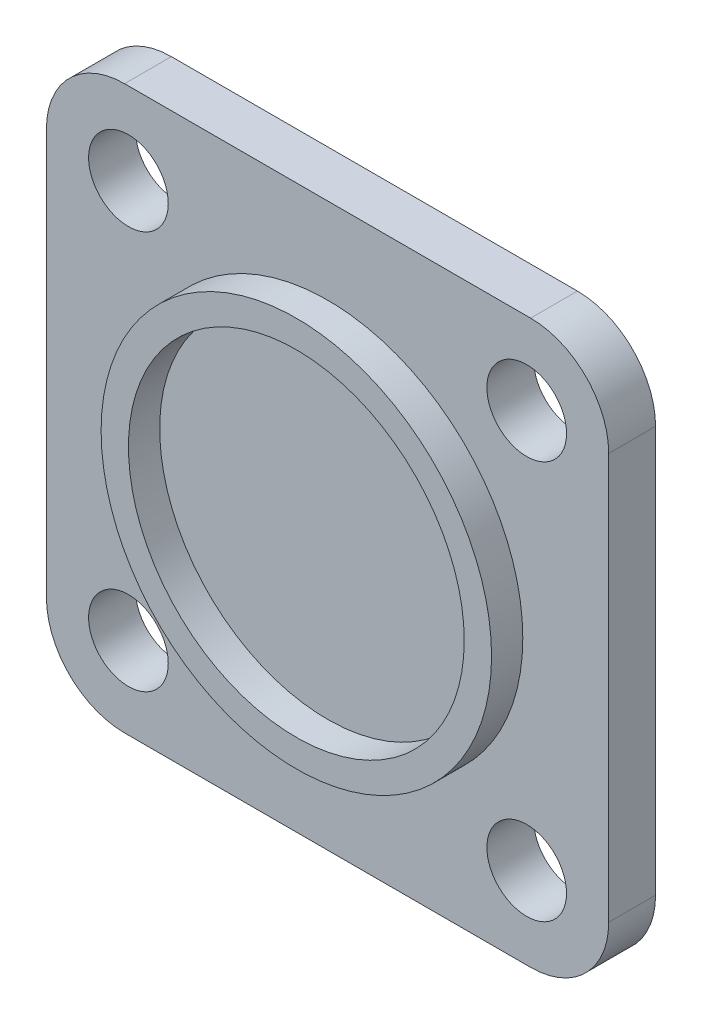
SolidWorks part; units mm, degrees
ref_plane "Płaszczyzna przednia" through (0, 0, 0) normal (0, 0, 1) x (1, 0, 0)
ref_plane "Płaszczyzna górna" through (0, 0, 0) normal (0, 1, 0) x (1, 0, 0)
ref_plane "Płaszczyzna prawa" through (0, 0, 0) normal (1, 0, 0) x (0, 0, -1)
sketch "Szkic1" plane through (0, 0, 0) normal (0, 0, 1) x (1, 0, 0)
  line L1 (-3.0269, 2.1836) -> (22.9731, 2.1836)
  line L2 (-8.0269, -2.8164) -> (-8.0269, -28.8164)
  line L3 (-3.0269, -33.8164) -> (22.9731, -33.8164)
  line L4 (27.9731, -2.8164) -> (27.9731, -28.8164)
  circle A2 centre (-2.7769, -3.0664) radius 2.55
  circle A3 centre (22.7231, -3.0664) radius 2.55
  circle A4 centre (-2.7769, -28.5664) radius 2.55
  circle A5 centre (22.7231, -28.5664) radius 2.55
  arc A6 (-3.0269, 2.1836) -> (-8.0269, -2.8164) centre (-3.0269, -2.8164) ccw
  arc A7 (22.9731, 2.1836) -> (27.9731, -2.8164) centre (22.9731, -2.8164) cw
  arc A8 (-8.0269, -28.8164) -> (-3.0269, -33.8164) centre (-3.0269, -28.8164) ccw
  arc A9 (22.9731, -33.8164) -> (27.9731, -28.8164) centre (22.9731, -28.8164) ccw
  point P6 (-8.0269, 2.1836)
  point P17 (27.9731, 2.1836)
  point P21 (-8.0269, -33.8164)
  dimension "D3" = 5
  dimension "D4" = 5
  dimension "D5" = 5
  dimension "D6" = 5
  dimension "D1" = 36
  dimension "D2" = 36
extrude "Dodanie-wyciągnięcie11" add sketch "Szkic1" along normal blind 3
sketch "Szkic7" plane through (0, 0, 3) normal (0, 0, 1) x (1, 0, 0)
  line L0 (-8.0269, -15.8164) -> (27.9731, -15.8164) construction
  line L5 (-8.0269, -2.8164) -> (-8.0269, -28.8164) construction
  line L6 (27.9731, -28.8164) -> (27.9731, -2.8164) construction
  line L8 (22.9731, 2.1836) -> (-3.0269, 2.1836) construction
  line L9 (9.9731, 2.1836) -> (9.9731, -33.8164) construction
  line L10 (-3.0269, -33.8164) -> (22.9731, -33.8164) construction
  circle A0 centre (9.9731, -15.8164) radius 12.5
  circle A1 centre (9.9731, -15.8164) radius 10.75
extrude "Dodanie-wyciągnięcie12" add sketch "Szkic7" along normal blind 2 contours A0 | A1
sketch "Sketch1" plane through (0, 0, 0) normal (0, 0, 1) x (1, 0, 0)
  line L4 (7.9731, -19.2805) -> (7.9731, -12.3523)
  line L6 (11.9731, -19.2805) -> (11.9731, -12.3523)
  arc A2 (7.9731, -19.2805) -> (11.9731, -19.2805) centre (9.9731, -15.8164) ccw
  arc A3 (11.9731, -12.3523) -> (7.9731, -12.3523) centre (9.9731, -15.8164) ccw
